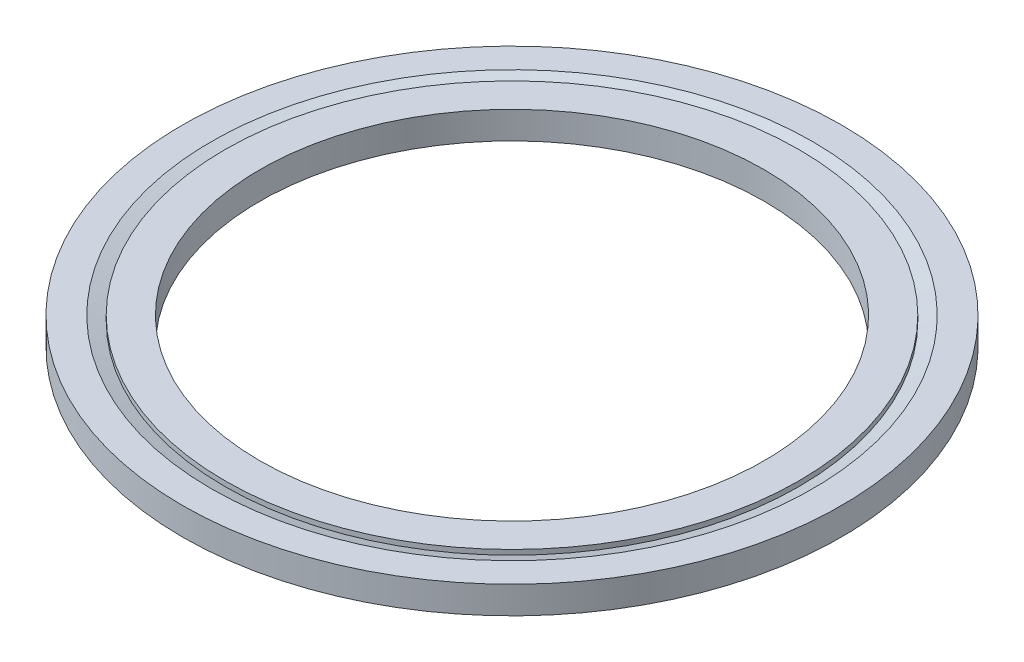
SolidWorks part; units mm, degrees
material "Copper"
ref_plane "Front Plane" through (0, 0, 0) normal (0, 0, 1) x (1, 0, 0)
ref_plane "Top Plane" through (0, 0, 0) normal (0, 1, 0) x (1, 0, 0)
ref_plane "Right Plane" through (0, 0, 0) normal (1, 0, 0) x (0, 0, -1)
sketch "Sketch1" plane through (0, 0, 0) normal (0, 0, 1) x (1, 0, 0)
  line L0 (0, 1) -> (0, -1) construction
  line L2 (0, 1) -> (24.0665, 1)
  line L3 (0, 1) -> (0, -1)
  line L4 (0, -1) -> (24.0665, -1)
  line L5 (24.0665, 1) -> (24.0665, -1)
  dimension "D3" = 2
  dimension "OD" = 48.133
revolve "Revolve1" add sketch "Sketch1" angle 360 about L0
sketch "Sketch2" plane through (0, 0, 0) normal (0, 0, 1) x (1, 0, 0)
  line L0 (-20.955, 0.635) -> (-20.955, 1.7999)
  line L1 (-20.955, 1.7999) -> (-24.1554, 1.7999)
  line L2 (-24.1554, 1.7999) -> (-20.955, 0.635)
  line L4 (0, 0) -> (0, 2.4004) construction
  line L5 (0, 0) -> (-11.7103, 0) construction
  line L6 (-24.1554, -1.7999) -> (-20.955, -0.635)
  line L7 (-20.955, -1.7999) -> (-24.1554, -1.7999)
  line L8 (-20.955, -0.635) -> (-20.955, -1.7999)
  dimension "D1" = 20
  dimension "D2" = 0.635
  dimension "Knife Length" = 3.2004
  dimension "Flange ID" = 24.1554
revolve "Cut-Revolve1" cut sketch "Sketch2" angle 360 about L4
sketch "Sketch3" plane through (0, 1, 0) normal (0, 1, 0) x (1, 0, 0)
  circle A0 centre (0, 0) radius 18.415
  dimension "ID" = 36.83
extrude "Cut-Extrude1" cut sketch "Sketch3" against normal through all
